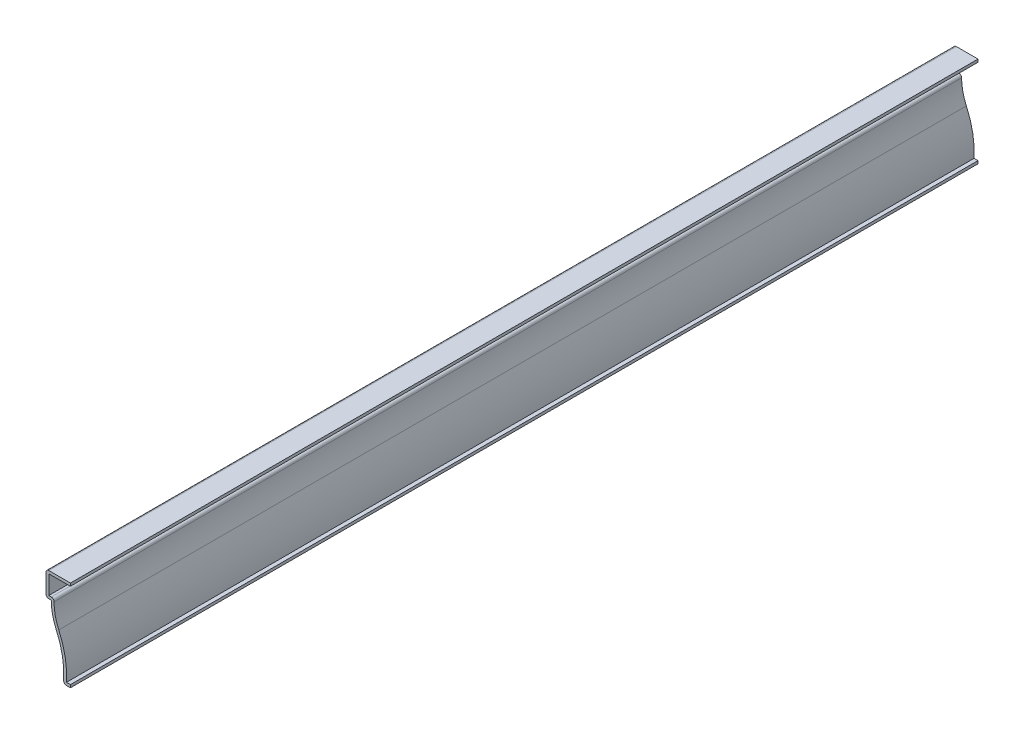
SolidWorks part; units mm, degrees
ref_plane "Front Plane" through (0, 0, 0) normal (0, 0, 1) x (1, 0, 0)
ref_plane "Top Plane" through (0, 0, 0) normal (0, 1, 0) x (1, 0, 0)
ref_plane "Right Plane" through (0, 0, 0) normal (1, 0, 0) x (0, 0, -1)
sketch "Sketch1" plane through (0, 0, 0) normal (0, 0, 1) x (1, 0, 0)
  line L0 (0, 0) -> (-3.175, 0)
  line L1 (-8.7312, 30.1625) -> (-11.1125, 30.1625)
  line L2 (-11.1125, 30.1625) -> (-11.1125, 41.275)
  line L3 (-11.1125, 41.275) -> (0, 41.275)
  arc A0 (-3.175, 0) -> (-6.4515, 19.6452) centre (-41.4932, 3.705) ccw
  arc A1 (-6.4515, 19.6452) -> (-8.7312, 30.1625) centre (16.6687, 30.1625) cw
  point P7 (0, 0)
  point P11 (-41.4507, 4.1206)
  point P12 (0, 0)
  dimension "D7" = 38.4969
  dimension "D8" = 25.4
  dimension "D1" = 41.275
  dimension "D2" = 11.1125
  dimension "D3" = 11.1125
  dimension "D4" = 2.3813
  dimension "D5" = 3.175
  dimension "D6" = 30.1625
extrude "Extrude-Thin1" add sketch "Sketch1" against normal blind 412.75 thin
fillet "Fillet1" radius 1.27 4 edges at (-3.175, 0, -206.375) (-7.4278, 31.4325, -206.375) (-11.1125, 30.1625, -206.375) (-11.1125, 41.275, -206.375)
